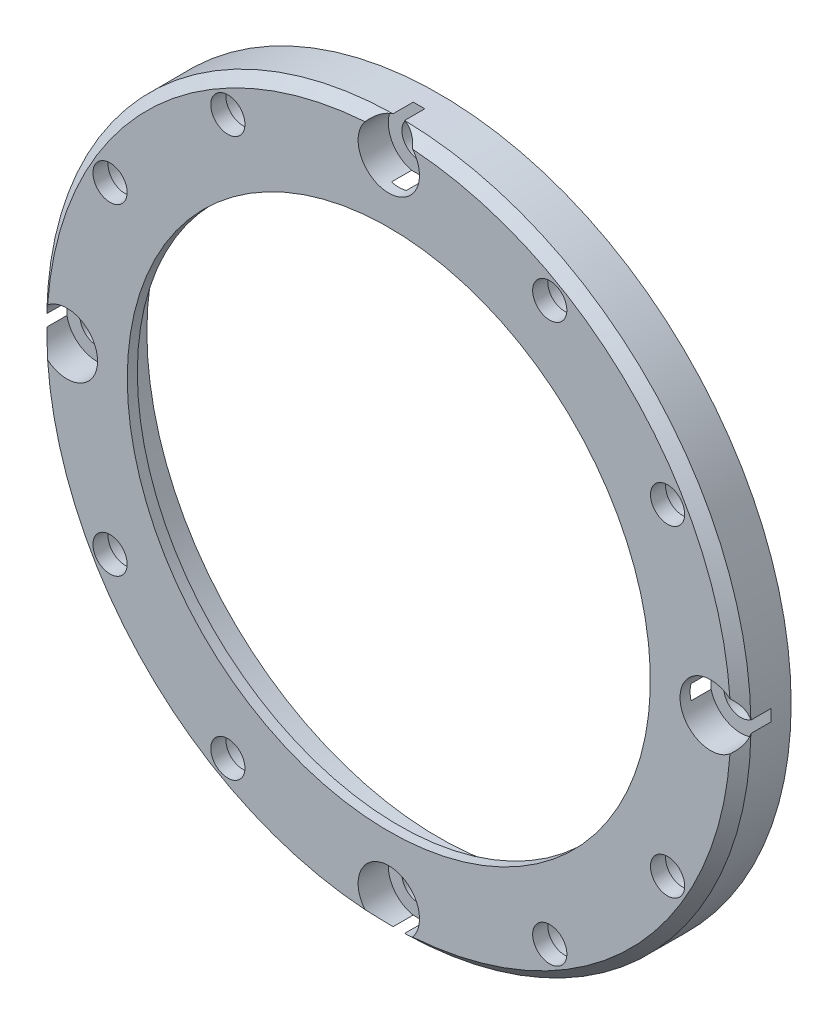
SolidWorks part; units mm, degrees
ref_plane "前视基准面" through (0, 0, 0) normal (0, 0, 1) x (1, 0, 0)
ref_plane "上视基准面" through (0, 0, 0) normal (0, 1, 0) x (1, 0, 0)
ref_plane "右视基准面" through (0, 0, 0) normal (1, 0, 0) x (0, 0, -1)
sketch "草图1" plane through (0, 0, 0) normal (0, 1, 0) x (1, 0, 0)
  line L0 (35, 5) -> (0, 5)
  line L1 (0, 5) -> (0, 0)
  line L2 (0, 0) -> (35, 0)
  line L3 (35, 0) -> (35, 5)
  line L4 (0, 5) -> (0, 0) construction
revolve "旋转1" add sketch "草图1" angle 360 about L4
hole_wizard "孔1" positions "草图3" profile "草图2" legacy
sketch "草图3" plane through (0, 0, -5) normal (0, 0, -1) x (-1, 0, 0)
  point P0 (16, -27.7128)
  point P1 (-16, -27.7128)
  point P2 (-27.7128, -16)
  point P3 (-27.7128, 16)
  point P4 (-16, 27.7128)
  point P5 (16, 27.7128)
  point P6 (27.7128, 16)
  point P7 (27.7128, -16)
sketch "草图2" plane through (-16, -27.7128, -5) normal (1, 0, 0) x (0, 1, 0)
  line L0 (0, 0) -> (0, 5)
  line L1 (0, 5) -> (1.7, 5)
  line L2 (1.7, 5) -> (1.7, 0)
  line L3 (1.7, 0) -> (0, 0)
  line L4 (0, 110) -> (0, -10) construction
  dimension "直径" = 3.4
  dimension "深度" = 5
hole_wizard "孔2" positions "草图5" profile "草图4" legacy
sketch "草图5" plane through (0, 0, -5) normal (0, 0, -1) x (-1, 0, 0)
  point P0 (0, 0)
sketch "草图4" plane through (0, 0, -5) normal (1, 0, 0) x (0, 1, 0)
  line L0 (0, 0) -> (0, 5)
  line L1 (0, 5) -> (26, 5)
  line L2 (26, 5) -> (26, 4)
  line L3 (26, 4) -> (29.05, 4)
  line L4 (29.05, 4) -> (29.05, 0)
  line L5 (29.05, 0) -> (0, 0)
  line L6 (0, 110) -> (0, -10) construction
  dimension "直径" = 52
  dimension "深度" = 5
  dimension "柱坑直径" = 58.1
  dimension "柱坑深度" = 4
hole_wizard "孔3" positions "草图7" profile "草图6" legacy
sketch "草图7" plane through (0, 0, 0) normal (0, 0, 1) x (1, 0, 0)
  point P0 (0, -32)
  point P1 (0, 32)
  point P2 (-32, 0)
  point P3 (32, 0)
sketch "草图6" plane through (0, -32, 0) normal (1, 0, 0) x (0, -1, 0)
  line L0 (0, 0) -> (0, 5)
  line L1 (0, 5) -> (1.7, 5)
  line L2 (1.7, 5) -> (1.7, 3)
  line L3 (1.7, 3) -> (3.05, 3)
  line L4 (3.05, 3) -> (3.05, 0)
  line L5 (3.05, 0) -> (0, 0)
  line L6 (0, 110) -> (0, -10) construction
  dimension "直径" = 3.4
  dimension "深度" = 5
  dimension "柱坑直径" = 6.1
  dimension "柱坑深度" = 3
chamfer "倒角1" distance 1 angle 45 4 edges at (-24.7487, 24.7487, 0) (-24.7487, -24.7487, 0) (24.7487, 24.7487, 0) (24.7487, -24.7487, 0)
sketch "草图8" plane through (0, 0, -5) normal (0, 0, -1) x (-1, 0, 0)
  circle A1 centre (-27.7128, 16) radius 2.2
  circle A2 centre (-16, 27.7128) radius 2.2
  circle A4 centre (16, 27.7128) radius 2.2
  circle A5 centre (27.7128, 16) radius 2.2
  circle A7 centre (27.7128, -16) radius 2.2
  circle A8 centre (16, -27.7128) radius 2.2
  circle A10 centre (-16, -27.7128) radius 2.2
  circle A11 centre (-27.7128, -16) radius 2.2
  point P27 (0, 0)
extrude "切除-拉伸1" cut sketch "草图8" against normal blind 3.5
